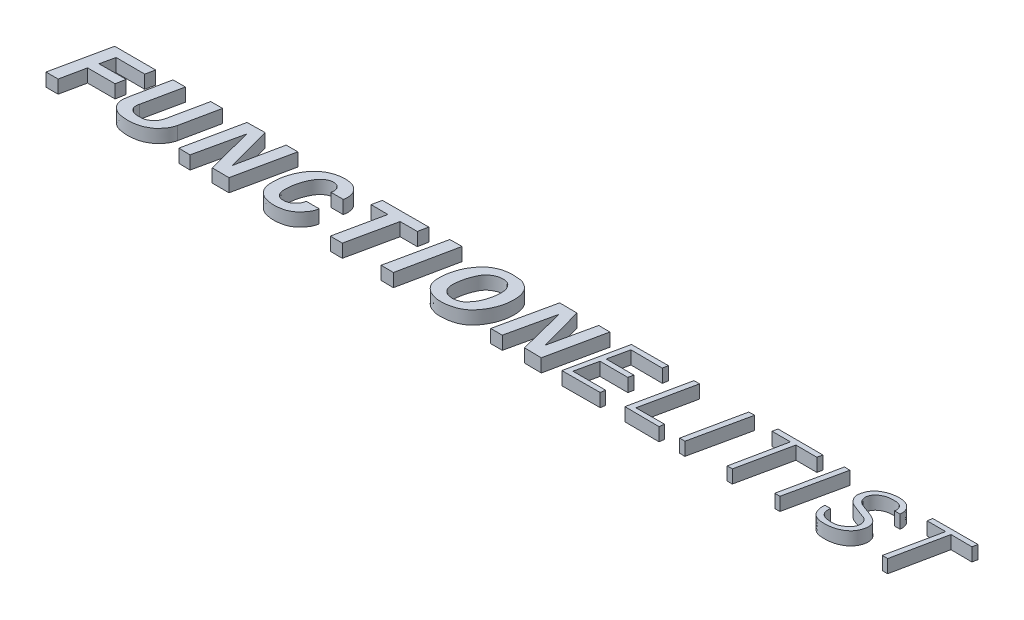
SolidWorks part; units mm, degrees
ref_plane "Front Plane" through (0, 0, 0) normal (0, 0, 1) x (1, 0, 0)
ref_plane "Top Plane" through (0, 0, 0) normal (0, 1, 0) x (1, 0, 0)
ref_plane "Right Plane" through (0, 0, 0) normal (1, 0, 0) x (0, 0, -1)
sketch "Sketch1" plane through (0, 0, 0) normal (0, 1, 0) x (1, 0, 0)
  line L0 (341.3333, 144) -> (1706.6667, 144) construction
sketch "Sketch2" plane through (0, 0, 0) normal (0, 1, 0) x (1, 0, 0)
  line L0 (330.2111, 175.5885) -> (353.316, 284.7914)
  line L1 (353.316, 284.7914) -> (432.4399, 284.6562)
  line L2 (432.4399, 284.6562) -> (428.788, 267.2083)
  line L3 (428.788, 267.2083) -> (373.4689, 267.3436)
  line L4 (373.4689, 267.3436) -> (367.5177, 240.428)
  line L5 (367.5177, 240.428) -> (419.5907, 240.5632)
  line L6 (419.5907, 240.5632) -> (416.3446, 222.5744)
  line L7 (416.3446, 222.5744) -> (363.3249, 222.5744)
  line L8 (363.3249, 222.5744) -> (353.5579, 175.6227)
  line L9 (353.5579, 175.6227) -> (330.2111, 175.5885)
  line L10 (465.5402, 284.7772) -> (450.7977, 211.9084)
  line L11 (465.5402, 284.7772) -> (489.466, 284.9356)
  line L12 (489.466, 284.9356) -> (474.1048, 212.2459)
  line L13 (523.0595, 212.9885) -> (538.157, 284.9845)
  line L14 (538.157, 284.9845) -> (560.9739, 285.0307)
  line L15 (560.9739, 285.0307) -> (545.9529, 212.7781)
  line L16 (585.218, 176.6305) -> (607.8886, 285.055)
  line L17 (607.8886, 285.055) -> (642.3873, 285.7121)
  line L18 (642.3873, 285.7121) -> (665.715, 199.6296)
  line L19 (665.715, 199.6296) -> (683.4572, 285.055)
  line L20 (683.4572, 285.055) -> (705.943, 285.055)
  line L21 (705.943, 285.055) -> (682.6356, 175.607)
  line L22 (682.6356, 175.607) -> (650.1723, 175.8324)
  line L23 (650.1723, 175.8324) -> (626.9521, 265.7826)
  line L24 (626.9521, 265.7826) -> (607.1135, 176.0579)
  line L25 (607.1135, 176.0579) -> (585.218, 176.6305)
  line L26 (796.5289, 210.6288) -> (821.3631, 210.5468)
  line L27 (829.0397, 249.3957) -> (805.3329, 249.3957)
  line L28 (868.3559, 285.5164) -> (864.5425, 267.4533)
  line L29 (864.5425, 267.4533) -> (897.2568, 267.2526)
  line L30 (897.2568, 267.2526) -> (877.7888, 175.7329)
  line L31 (877.7888, 175.7329) -> (901.0702, 175.5322)
  line L32 (901.0702, 175.5322) -> (920.7389, 267.2526)
  line L33 (920.7389, 267.2526) -> (953.8546, 267.2526)
  line L34 (953.8546, 267.2526) -> (957.4672, 285.7171)
  line L35 (957.4672, 285.7171) -> (868.3559, 285.5164)
  line L36 (998.611, 285.115) -> (1021.9137, 285.3133)
  line L37 (1021.9137, 285.3133) -> (999.2617, 175.7187)
  line L38 (999.2617, 175.7187) -> (975.3742, 176.0862)
  line L39 (975.3742, 176.0862) -> (998.611, 285.115)
  line L40 (1186.3938, 176.1072) -> (1208.712, 176.1072)
  line L41 (1208.712, 176.1072) -> (1228.6102, 265.6488)
  line L42 (1228.6102, 265.6488) -> (1251.1972, 176.3761)
  line L43 (1251.1972, 176.3761) -> (1284.0023, 175.8383)
  line L44 (1284.0023, 175.8383) -> (1307.1141, 285.0217)
  line L45 (1307.1141, 285.0217) -> (1285.3987, 285.1954)
  line L46 (1285.3987, 285.1954) -> (1266.727, 199.9923)
  line L47 (1266.727, 199.9923) -> (1243.6682, 285.0091)
  line L48 (1243.6682, 285.0091) -> (1210.0565, 285.278)
  line L49 (1210.0565, 285.278) -> (1186.3938, 176.1072)
  line L50 (1348.6, 285.0217) -> (1325.1793, 174.4301)
  line L51 (1325.1793, 174.4301) -> (1398.6719, 174.8339)
  line L52 (1398.6719, 174.8339) -> (1400.0852, 183.9195)
  line L53 (1400.0852, 183.9195) -> (1336.8897, 183.9195)
  line L54 (1336.8897, 183.9195) -> (1346.3791, 226.7229)
  line L55 (1346.3791, 226.7229) -> (1400.0852, 226.521)
  line L56 (1400.0852, 226.521) -> (1402.1043, 236.2123)
  line L57 (1402.1043, 236.2123) -> (1348.6, 236.4142)
  line L58 (1348.6, 236.4142) -> (1357.08, 275.5834)
  line L59 (1357.08, 275.5834) -> (1417.8527, 275.1796)
  line L60 (1417.8527, 275.1796) -> (1419.6698, 285.2747)
  line L61 (1419.6698, 285.2747) -> (1348.6, 285.0217)
  line L62 (1469.1693, 284.7234) -> (1479.9982, 285.0084)
  line L63 (1479.9982, 285.0084) -> (1458.6253, 183.5585)
  line L64 (1458.6253, 183.5585) -> (1513.6248, 183.8435)
  line L65 (1513.6248, 183.8435) -> (1512.2, 174.4394)
  line L66 (1512.2, 174.4394) -> (1446.0866, 175.0094)
  line L67 (1446.0866, 175.0094) -> (1469.1693, 284.7234)
  line L68 (1574.3237, 285.2933) -> (1585.4376, 285.5783)
  line L69 (1585.4376, 285.5783) -> (1561.5, 175.0094)
  line L70 (1561.5, 175.0094) -> (1551.241, 175.2944)
  line L71 (1551.241, 175.2944) -> (1574.3237, 285.2933)
  line L72 (1630.831, 285.2343) -> (1628.9068, 275.6132)
  line L73 (1628.9068, 275.6132) -> (1664.3124, 275.6132)
  line L74 (1664.3124, 275.6132) -> (1643.5308, 174.5917)
  line L75 (1643.5308, 174.5917) -> (1653.3443, 174.5917)
  line L76 (1653.3443, 174.5917) -> (1674.8956, 275.6132)
  line L77 (1674.8956, 275.6132) -> (1715.3041, 275.4208)
  line L78 (1715.3041, 275.4208) -> (1717.4208, 285.0418)
  line L79 (1717.4208, 285.0418) -> (1630.831, 285.2343)
  line L80 (1758.2142, 285.8115) -> (1768.7974, 285.4267)
  line L81 (1768.7974, 285.4267) -> (1744.9371, 174.5917)
  line L82 (1744.9371, 174.5917) -> (1734.9312, 174.7842)
  line L83 (1734.9312, 174.7842) -> (1758.2142, 285.8115)
  line L84 (1803.3489, 203.1451) -> (1814.3877, 203.1451)
  line L85 (1879.4979, 260.7714) -> (1890.2871, 260.76)
  line L86 (1929.083, 284.8573) -> (1927.7045, 275.4578)
  line L87 (1927.7045, 275.4578) -> (1963.5477, 275.5831)
  line L88 (1963.5477, 275.5831) -> (1942.2137, 174.6813)
  line L89 (1942.2137, 174.6813) -> (1952.6164, 174.5368)
  line L90 (1952.6164, 174.5368) -> (1973.4653, 275.6981)
  line L91 (1973.4653, 275.6981) -> (2014.1252, 275.3296)
  line L92 (2014.1252, 275.3296) -> (2016.0906, 285.1568)
  line L93 (2016.0906, 285.1568) -> (1929.083, 284.8573)
  spline S0 degree 3 poles (450.7977, 211.9084) (450.4017, 209.9511) (449.7175, 204.1575) (449.8524, 197.9595) (452.9167, 189.1621) (457.1056, 184.2395) (463.3109, 178.8872) (471.3713, 175.3823) (480.944, 174.2199) (490.7418, 173.3643) (501.4277, 174.4685) (510.9696, 176.4632) (519.0882, 180.1283) (524.3819, 183.4164) (529.8527, 186.5674) (533.6828, 191.2136) (537.987, 195.9892) (541.8308, 201.4895) (544.3331, 207.382) (545.6252, 211.2017) (545.9529, 212.7781) knots 0 0 0 0 0.043908 0.110716 0.159393 0.219822 0.270449 0.330055 0.40784 0.477215 0.542146 0.639163 0.686234 0.733612 0.774061 0.821315 0.862079 0.913354 0.965139 1 1 1 1
  spline S1 degree 3 poles (474.1048, 212.2459) (473.8201, 210.8987) (473.3419, 208.2397) (473.3912, 204.3207) (473.8723, 200.2725) (476.1726, 196.8205) (479.4263, 193.9093) (483.9965, 191.4205) (490.1815, 190.6811) (497.0565, 190.8884) (503.5345, 191.2826) (508.9399, 193.8384) (513.2584, 196.4594) (516.9534, 200.1702) (519.8174, 204.1392) (521.9247, 208.5867) (522.7428, 211.4781) (523.0595, 212.9885) knots 0 0 0 0 0.055066 0.10659 0.156186 0.21469 0.266458 0.329688 0.418336 0.509804 0.60535 0.672337 0.745495 0.805586 0.87941 0.939581 1 1 1 1
  spline S2 degree 3 poles (796.5289, 210.6288) (796.1363, 207.1439) (794.3171, 202.516) (789.8472, 197.3861) (786.1933, 193.6392) (780.216, 190.8971) (773.2736, 189.833) (765.801, 190.6177) (760.0664, 195.0353) (756.05, 202.066) (755.9784, 212.8374) (757.0322, 225.0195) (760.3494, 238.5971) (765.0529, 249.3727) (770.5975, 258.1544) (776.4048, 263.7869) (783.241, 267.6805) (789.9855, 269.1725) (795.6193, 268.3702) (800.0235, 266.9015) (805.7623, 261.2706) (806.7965, 254.3377) (805.3329, 249.3957) knots 0 0 0 0 0.063236 0.086132 0.122714 0.156521 0.202501 0.248775 0.287135 0.328458 0.390432 0.476348 0.550173 0.641096 0.687261 0.736692 0.785332 0.827671 0.858232 0.887348 0.909466 1 1 1 1
  spline S3 degree 3 poles (821.3631, 210.5468) (820.7759, 205.0843) (817.8397, 198.3323) (811.6556, 190.4476) (807.2181, 185.3424) (800.2844, 180.06) (792.9752, 176.0822) (782.8177, 174.009) (773.328, 172.5888) (763.0901, 173.5299) (754.8159, 175.2109) (747.04, 178.2575) (740.8374, 183.4206) (735.7505, 189.8116) (732.0775, 199.6293) (731.6477, 212.1872) (732.8293, 225.6944) (735.6766, 236.0953) (738.8518, 245.1976) (742.366, 252.2375) (747.3731, 260.7218) (753.5973, 267.5486) (763.32, 276.6528) (777.3237, 283.1948) (794.2968, 286.2989) (808.0679, 284.7698) (816.8946, 281.2253) (821.7968, 276.9281) (825.5795, 272.6891) (828.5348, 267.303) (830.251, 259.4855) (830.1466, 253.3079) (829.0397, 249.3957) knots 0 0 0 0 0.054999 0.072083 0.101177 0.12285 0.159869 0.18376 0.227112 0.256099 0.286963 0.312225 0.339402 0.36739 0.393756 0.443632 0.492576 0.530285 0.552055 0.589796 0.609452 0.651289 0.682399 0.743437 0.803856 0.854689 0.881272 0.898176 0.919988 0.938384 0.959446 1 1 1 1
  spline S4 degree 3 poles (1103.8619, 173.4489) (1094.439, 172.9151) (1085.1584, 172.8895) (1076.8175, 175.5037) (1068.3455, 178.4042) (1061.5046, 184.0406) (1054.691, 192.4485) (1052.1026, 202.2724) (1052.0166, 212.1512) (1052.1886, 219.6143) (1053.8481, 228.6146) (1056.261, 238.8922) (1061.525, 251.8421) (1068.4531, 262.3245) (1076.8783, 272.4151) (1085.8779, 279.0065) (1097.477, 284.3368) (1108.0988, 286.7045) (1118.9103, 287.3951) (1128.3104, 286.4839) (1137.4022, 285.6791) (1144.816, 281.6234) (1153.0263, 275.7679) (1158.2628, 266.1573) (1160.627, 255.6425) (1161.1536, 246.5363) (1160.6084, 237.0278) (1158.724, 227.1312) (1155.94, 218.0918) (1151.8727, 208.9954) (1145.8612, 198.5265) (1137.3718, 188.2589) (1127.672, 181.1365) (1119.964, 177.7065) (1112.1312, 175.2645) (1103.8619, 173.4489) (1094.439, 172.9151) (1085.1584, 172.8895) knots -0.071117 -0.053946 -0.025689 0 0.02573 0.051932 0.073305 0.10082 0.125326 0.163809 0.183249 0.2089 0.226567 0.260388 0.297882 0.343868 0.365822 0.408625 0.436522 0.473174 0.499739 0.527561 0.553082 0.575613 0.597856 0.637572 0.663955 0.688712 0.714253 0.744181 0.773516 0.793866 0.828166 0.875214 0.905069 0.928883 0.946054 0.974311 1 1.02573 1.051932 1.073305 only from (1094.4272, 172.9971) to (1094.4272, 172.9971)
  spline S5 degree 3 poles (1098.3695, 189.4106) (1095.3399, 189.7268) (1089.5062, 190.4296) (1083.4171, 193.8969) (1080.7246, 197.7439) (1078.0719, 201.3562) (1076.6339, 207.0036) (1075.8972, 214.9744) (1077.5134, 224.2323) (1079.0801, 234.1743) (1082.3795, 243.4663) (1086.2775, 252.7299) (1092.1955, 261.5782) (1100.0822, 266.5583) (1107.923, 270.0269) (1116.1889, 270.9269) (1125.3016, 269.8062) (1131.3922, 264.2991) (1135.0861, 258.7006) (1137.0011, 252.3913) (1137.069, 244.8125) (1136.75, 235.2516) (1133.9869, 223.9899) (1130.3671, 213.1486) (1124.6248, 203.4047) (1118.3992, 196.7173) (1113.5937, 192.5489) (1111.5789, 191.8488) knots 0 0 0 0 0.047624 0.076067 0.09669 0.11317 0.138968 0.177316 0.22569 0.270714 0.319286 0.364189 0.412774 0.466538 0.493207 0.533135 0.583074 0.616439 0.645307 0.677257 0.707726 0.75189 0.81196 0.870512 0.912744 0.970141 1 1 1 1
  spline S6 degree 3 poles (1098.3695, 189.4106) (1099.779, 189.2634) (1105.6107, 190.0723) (1109.5132, 191.131) (1111.5789, 191.8488) knots 0 0 0 0 0.517019 1 1 1 1
  spline S7 degree 3 poles (1803.3489, 203.1451) (1802.6292, 198.4218) (1803.681, 190.7851) (1807.5777, 180.8969) (1814.0087, 175.6532) (1821.6636, 172.3278) (1831.3398, 171.836) (1844.4565, 172.1017) (1859.4844, 176.4607) (1873.1891, 185.9872) (1879.633, 198.3386) (1881.5847, 209.6969) (1879.1288, 220.7248) (1869.0038, 228.6604) (1856.1004, 233.3913) (1843.5772, 237.5563) (1832.6908, 242.8459) (1828.276, 251.9557) (1828.9024, 261.2147) (1833.9679, 268.7104) (1841.1728, 273.7262) (1849.5448, 277.2737) (1858.4776, 277.8738) (1866.7585, 277.9379) (1873.3548, 276.2158) (1879.4349, 270.8262) (1880.8161, 264.6323) (1879.4979, 260.7714) knots 0 0 0 0 0.053085 0.086629 0.116685 0.143953 0.179636 0.224613 0.291952 0.353162 0.407421 0.444038 0.482182 0.528076 0.581277 0.637462 0.678446 0.712599 0.744697 0.778972 0.810628 0.842933 0.880225 0.910512 0.936616 0.954688 1 1 1 1
  spline S8 degree 3 poles (1814.3877, 203.1451) (1813.6026, 199.3144) (1813.5239, 192.5808) (1818.9982, 185.0498) (1826.9692, 181.9336) (1836.6581, 180.7377) (1847.9512, 181.3736) (1858.2122, 186.9809) (1866.8026, 194.7328) (1870.7863, 206.2592) (1865.9017, 219.0149) (1853.3602, 222.2769) (1843.2736, 226.0961) (1834.7549, 229.5926) (1827.4754, 232.7844) (1821.4303, 239.0821) (1816.0421, 247.8042) (1818.0877, 258.8642) (1821.819, 268.8971) (1828.8179, 276.6956) (1837.805, 282.0301) (1847.7385, 285.878) (1859.2165, 287.4684) (1871.2149, 287.1521) (1882.392, 282.7762) (1889.9227, 272.9989) (1890.9987, 265.0188) (1890.2871, 260.76) knots 0 0 0 0 0.044977 0.071796 0.100101 0.139122 0.182784 0.225458 0.269246 0.311511 0.356589 0.405222 0.448856 0.480892 0.509756 0.537719 0.579265 0.619545 0.6592 0.700614 0.73502 0.777219 0.820574 0.865625 0.912641 0.951111 1 1 1 1
  point P0 (330.2111, 175.5885)
  point P1 (353.316, 284.7914)
  point P2 (432.4399, 284.6562)
  point P3 (428.788, 267.2083)
  point P4 (373.4689, 267.3436)
  point P5 (367.5177, 240.428)
  point P6 (419.5907, 240.5632)
  point P7 (416.3446, 222.5744)
  point P8 (363.3249, 222.5744)
  point P9 (353.5579, 175.6227)
  point P10 (465.5402, 284.7772)
  point P11 (489.466, 284.9356)
  point P12 (474.1048, 212.2459)
  point P13 (523.0595, 212.9885)
  point P14 (538.157, 284.9845)
  point P15 (560.9739, 285.0307)
  point P16 (545.9529, 212.7781)
  point P17 (450.7977, 211.9084)
  point P18 (585.218, 176.6305)
  point P19 (607.8886, 285.055)
  point P20 (642.3873, 285.7121)
  point P21 (665.715, 199.6296)
  point P22 (683.4572, 285.055)
  point P23 (705.943, 285.055)
  point P24 (682.6356, 175.607)
  point P25 (650.1723, 175.8324)
  point P26 (626.9521, 265.7826)
  point P27 (607.1135, 176.0579)
  point P28 (829.0397, 249.3957)
  point P29 (805.3329, 249.3957)
  point P30 (796.5289, 210.6288)
  point P31 (821.3631, 210.5468)
  point P32 (868.3559, 285.5164)
  point P33 (957.4672, 285.7171)
  point P34 (953.8546, 267.2526)
  point P35 (864.5425, 267.4533)
  point P36 (897.2568, 267.2526)
  point P37 (920.7389, 267.2526)
  point P38 (901.0702, 175.5322)
  point P39 (877.7888, 175.7329)
  point P40 (998.611, 285.115)
  point P41 (1021.9137, 285.3133)
  point P42 (999.2617, 175.7187)
  point P43 (975.3742, 176.0862)
  point P44 (1210.0565, 285.278)
  point P45 (1243.6682, 285.0091)
  point P46 (1186.3938, 176.1072)
  point P47 (1208.712, 176.1072)
  point P48 (1228.6102, 265.6488)
  point P49 (1251.1972, 176.3761)
  point P50 (1284.0023, 175.8383)
  point P51 (1285.3987, 285.1954)
  point P52 (1307.1141, 285.0217)
  point P53 (1266.727, 199.9923)
  point P54 (1348.6, 285.0217)
  point P55 (1419.6698, 285.2747)
  point P56 (1417.8527, 275.1796)
  point P57 (1357.08, 275.5834)
  point P58 (1348.6, 236.4142)
  point P59 (1402.1043, 236.2123)
  point P60 (1400.0852, 226.521)
  point P61 (1346.3791, 226.7229)
  point P62 (1336.8897, 183.9195)
  point P63 (1398.6719, 174.8339)
  point P64 (1400.0852, 183.9195)
  point P65 (1325.1793, 174.4301)
  point P66 (1469.1693, 284.7234)
  point P67 (1446.0866, 175.0094)
  point P68 (1512.2, 174.4394)
  point P69 (1513.6248, 183.8435)
  point P70 (1458.6253, 183.5585)
  point P71 (1479.9982, 285.0084)
  point P72 (1574.3237, 285.2933)
  point P73 (1585.4376, 285.5783)
  point P74 (1561.5, 175.0094)
  point P75 (1551.241, 175.2944)
  point P76 (1630.831, 285.2343)
  point P77 (1628.9068, 275.6132)
  point P78 (1664.3124, 275.6132)
  point P79 (1674.8956, 275.6132)
  point P80 (1715.3041, 275.4208)
  point P81 (1717.4208, 285.0418)
  point P82 (1643.5308, 174.5917)
  point P83 (1653.3443, 174.5917)
  point P84 (1734.9312, 174.7842)
  point P85 (1744.9371, 174.5917)
  point P86 (1768.7974, 285.4267)
  point P87 (1758.2142, 285.8115)
  point P88 (1803.3489, 203.1451)
  point P89 (1814.3877, 203.1451)
  point P90 (1879.4979, 260.7714)
  point P91 (1890.2871, 260.76)
  point P92 (1927.7045, 275.4578)
  point P93 (1963.5477, 275.5831)
  point P94 (1929.083, 284.8573)
  point P95 (2016.0906, 285.1568)
  point P96 (2014.1252, 275.3296)
  point P97 (1973.4653, 275.6981)
  point P98 (1942.2137, 174.6813)
  point P99 (1952.6164, 174.5368)
extrude "Boss-Extrude1" add sketch "Sketch2" along normal blind 25.4
